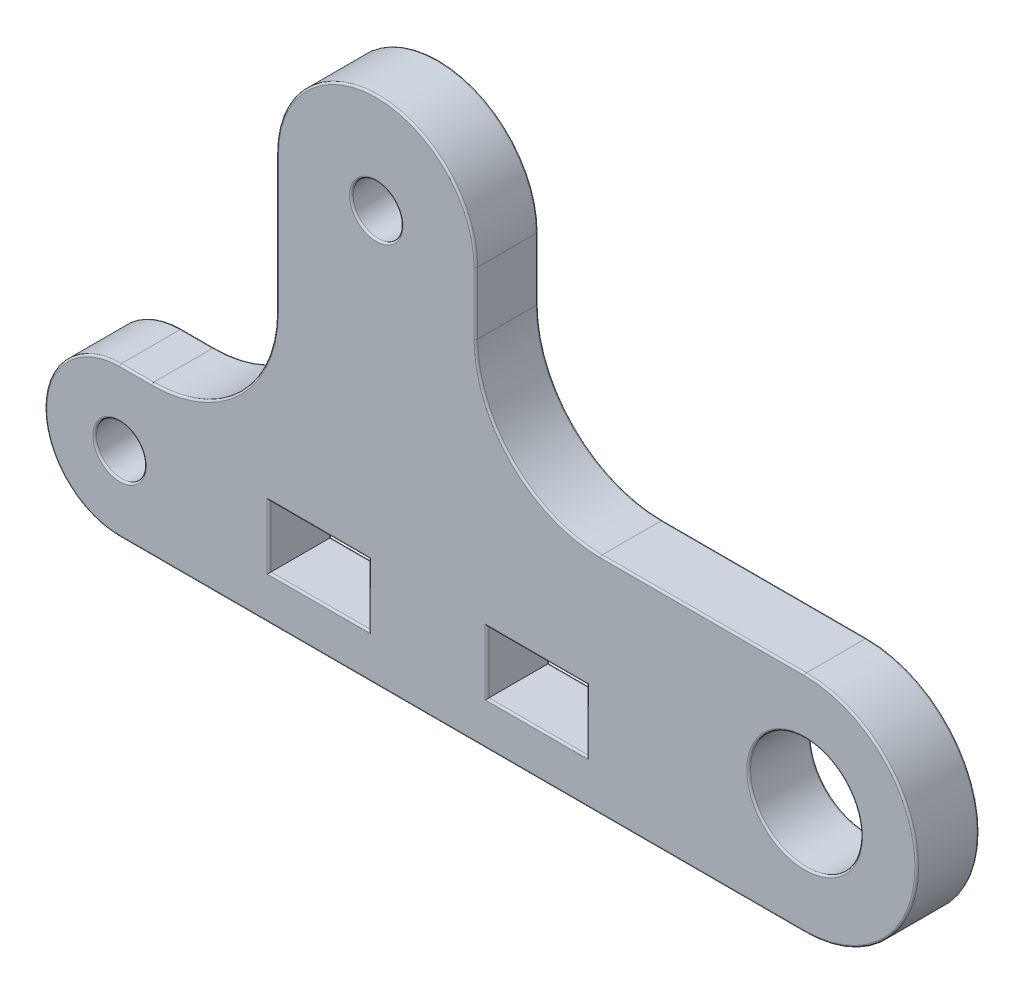
SolidWorks part; units mm, degrees
ref_plane "Płaszczyzna przednia" through (0, 0, 0) normal (0, 0, 1) x (1, 0, 0)
ref_plane "Płaszczyzna górna" through (0, 0, 0) normal (0, 1, 0) x (1, 0, 0)
ref_plane "Płaszczyzna prawa" through (0, 0, 0) normal (1, 0, 0) x (0, 0, -1)
sketch "Szkic1" plane through (0, 0, 0) normal (0, 0, 1) x (1, 0, 0)
  line L0 (-27.5, 0) -> (27.5, 0)
  line L1 (-27.5, 12) -> (-24.9, 12)
  line L2 (-14.9, 22) -> (-14.9, 33)
  line L3 (1.1, 33) -> (1.1, 28)
  line L4 (11.1, 18) -> (27.5, 18)
  line L5 (-27.5, 6) -> (-15.5, 6) construction
  line L7 (-15.5, 3.5) -> (-7.5, 3.5)
  line L8 (-15.5, 3.5) -> (-15.5, 8.5)
  line L9 (-15.5, 8.5) -> (-7.5, 8.5)
  line L10 (-7.5, 3.5) -> (-7.5, 8.5)
  line L15 (2, 3.5) -> (10, 3.5)
  line L16 (2, 3.5) -> (2, 8.5)
  line L17 (2, 8.5) -> (10, 8.5)
  line L18 (10, 3.5) -> (10, 8.5)
  arc A0 (-27.5, 0) -> (-27.5, 12) centre (-27.5, 6) cw
  arc A1 (27.5, 0) -> (27.5, 18) centre (27.5, 9) ccw
  circle A2 centre (-27.5, 6) radius 2
  circle A3 centre (27.5, 9) radius 4.5
  circle A4 centre (-6.9, 33) radius 2
  circle A5 centre (-6.9, 33) radius 8 construction
  arc A6 (-14.9, 33) -> (1.1, 33) centre (-6.9, 33) cw
  arc A7 (-14.9, 22) -> (-24.9, 12) centre (-24.9, 22) cw
  arc A8 (11.1, 18) -> (1.1, 28) centre (11.1, 28) cw
  dimension "D2" = 6
  dimension "D3" = 9
  dimension "D4" = 4
  dimension "D5" = 9
  dimension "D6" = 33
  dimension "D8" = 16
  dimension "D9" = 10
  dimension "D10" = 10
  dimension "D1" = 55
  dimension "D7" = 6.9
  dimension "D11" = 12
  dimension "D12" = 8
  dimension "D13" = 5
  dimension "D14" = 9.5
extrude "Dodanie-wyciągnięcie1" add sketch "Szkic1" along normal mid plane 5
fillet "Zaokrąglenie1" radius 0.15 42 edges at (10, 6, -2.5) (6, 3.5, -2.5) (2, 6, -2.5) (6, 8.5, -2.5) (-7.5, 6, -2.5) (-11.5, 3.5, -2.5) (-15.5, 6, -2.5) (-11.5, 8.5, -2.5) (-4.9, 33, -2.5) (32, 9, -2.5) (0, 0, -2.5) (36.5, 9, -2.5) (19.3, 18, -2.5) (4.0289, 20.9289, -2.5) (1.1, 30.5, -2.5) (-6.9, 41, -2.5) (-14.9, 27.5, -2.5) (-17.8289, 14.9289, -2.5) (-26.2, 12, -2.5) (-33.5, 6, -2.5) (-25.5, 6, -2.5) (6, 3.5, 2.5) (10, 6, 2.5) (6, 8.5, 2.5) (2, 6, 2.5) (-4.9, 33, 2.5) (-25.5, 6, 2.5) (32, 9, 2.5) (-26.2, 12, 2.5) (-17.8289, 14.9289, 2.5) (-14.9, 27.5, 2.5) (-6.9, 41, 2.5) (1.1, 30.5, 2.5) (4.0289, 20.9289, 2.5) (19.3, 18, 2.5) (36.5, 9, 2.5) (0, 0, 2.5) (-33.5, 6, 2.5) (-11.5, 3.5, 2.5) (-7.5, 6, 2.5) (-11.5, 8.5, 2.5) (-15.5, 6, 2.5)
